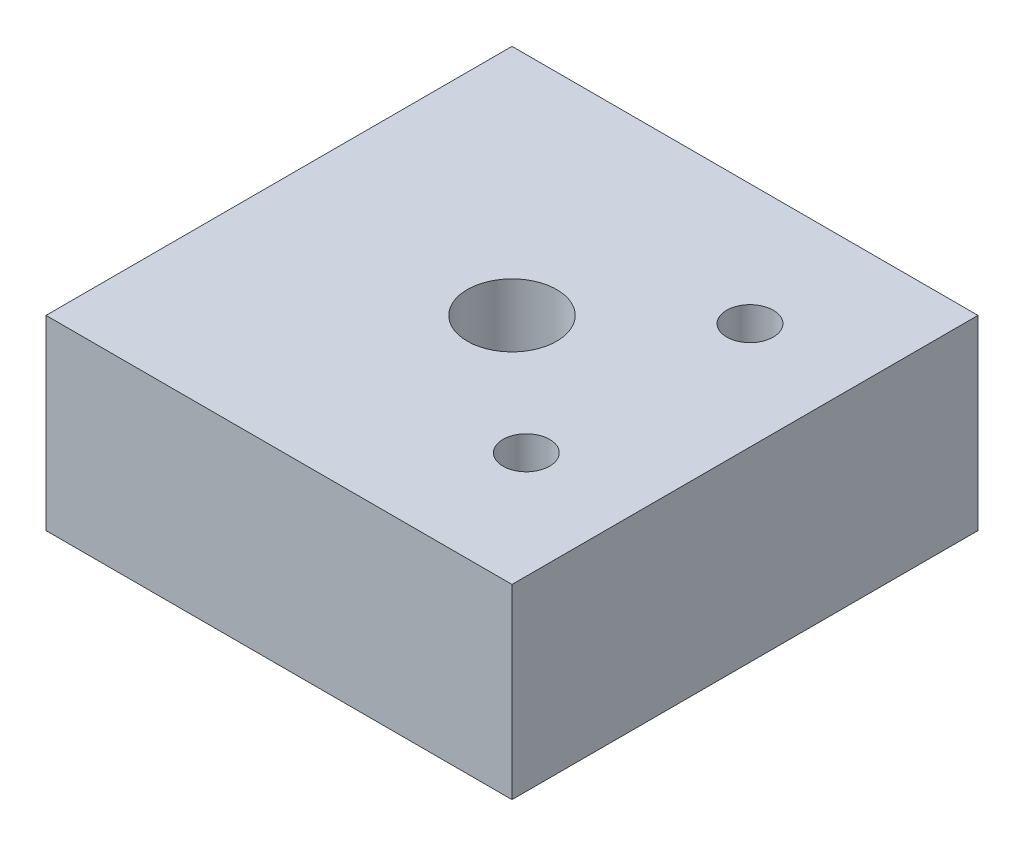
SolidWorks part; units mm, degrees
ref_plane "Front Plane" through (0, 0, 0) normal (0, 0, 1) x (1, 0, 0)
ref_plane "Top Plane" through (0, 0, 0) normal (0, 1, 0) x (1, 0, 0)
ref_plane "Right Plane" through (0, 0, 0) normal (1, 0, 0) x (0, 0, -1)
sketch "Sketch1" plane through (0, 0, 0) normal (0, 1, 0) x (1, 0, 0)
  line L1 (-250, -250) -> (250, -250)
  line L2 (-250, -250) -> (-250, 250)
  line L3 (-250, 250) -> (250, 250)
  line L4 (250, -250) -> (250, 250)
  line L5 (-250, -250) -> (250, 250) construction
  line L6 (-250, 250) -> (250, -250) construction
  circle A0 centre (0, 0) radius 48.0194
  circle A1 centre (135.3569, 120) radius 25
  circle A2 centre (135.3569, -120) radius 25
  point P0 (0, 0)
  dimension "D5" = 50
  dimension "D6" = 50
  dimension "D1" = 500
  dimension "D2" = 500
  dimension "D3" = 130
  dimension "D4" = 130
extrude "Boss-Extrude1" add sketch "Sketch1" along normal blind 200
